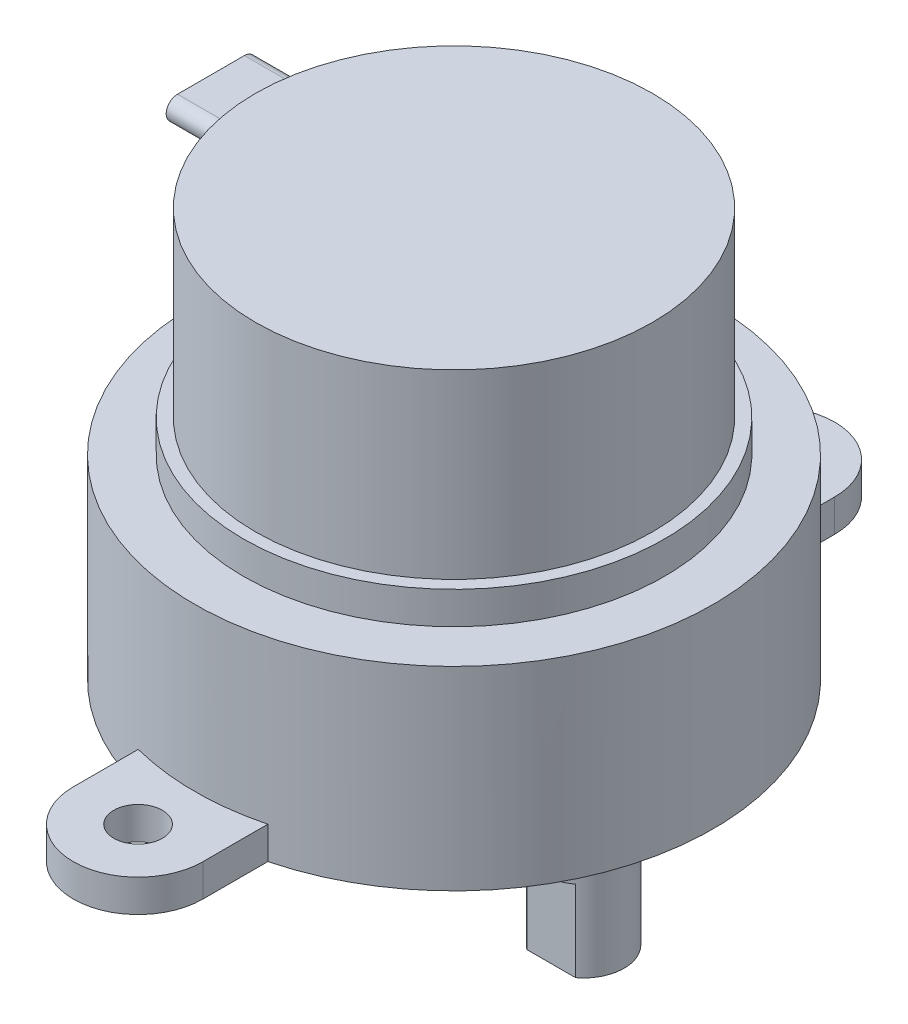
SolidWorks part; units mm, degrees
ref_plane "Front Plane" through (0, 0, 0) normal (0, 0, 1) x (1, 0, 0)
ref_plane "Top Plane" through (0, 0, 0) normal (0, 1, 0) x (1, 0, 0)
ref_plane "Right Plane" through (0, 0, 0) normal (1, 0, 0) x (0, 0, -1)
sketch "Sketch1" plane through (0, 0, 0) normal (0, 0, 1) x (1, 0, 0)
  line L0 (0, 0) -> (-21, 0) construction
  line L1 (0, 0) -> (0, 32.25) construction
  line L2 (0, 0) -> (-16, 0)
  line L3 (-16, 0) -> (-16, 12)
  line L4 (-16, 12) -> (-13, 12)
  line L5 (-13, 12) -> (-13, 14)
  line L6 (-13, 14) -> (-12.25, 14)
  line L7 (-12.25, 14) -> (-12.25, 25.2)
  line L8 (-12.25, 25.2) -> (0, 25.2)
  line L9 (0, 0) -> (0, 25.2)
  point P3 (-13, 13)
  dimension "D1" = 26
  dimension "D2" = 24.5
  dimension "D3" = 32
  dimension "D4" = 11.2
  dimension "D5" = 25.2
  dimension "D6" = 2
  dimension "D7" = 12
revolve "Revolve1" add sketch "Sketch1" angle 360 about L9
sketch "Sketch2" plane through (0, 0, 0) normal (0, 0, 1) x (1, 0, 0)
  line L0 (8, 0) -> (8, -10.2) construction
  line L1 (-16, 0) -> (16, 0) construction
  line L2 (4, -2.7) -> (4, -1.25)
  line L3 (4, -1.25) -> (3.5, -1.25)
  line L4 (3.5, -1.25) -> (3.5, 0)
  line L5 (4, -2.7) -> (5.5, -2.7)
  line L6 (5.5, -2.7) -> (5.5, -10.2)
  line L7 (5.5, -10.2) -> (8, -10.2)
  line L8 (3.5, 0) -> (8, 0)
  line L9 (8, 0) -> (8, -10.2)
  dimension "D1" = 5
  dimension "D2" = 8
  dimension "D3" = 8
  dimension "D4" = 2.7
  dimension "D5" = 10.2
  dimension "D6" = 9
  dimension "D7" = 1.25
revolve "Revolve2" add sketch "Sketch2" angle 360 about L0
hole_wizard "M3 Tapped Hole1" positions "Sketch3" profile "Sketch4" tap size "M3" standard "GB"
sketch "Sketch3" plane through (0, -10.2, 0) normal (0, -1, 0) x (-1, 0, 0)
  point P0 (-8, 0)
cosmetic thread "Hole Thread1" parameters "D1"=6, "D2"=3
sketch "Sketch4" plane through (8, -10.2, 0) normal (1, 0, 0) x (0, 0, -1)
  line L0 (0, 0) -> (0, 8.2511)
  line L1 (0, 8.2511) -> (1.25, 7.5)
  line L2 (1.25, 7.5) -> (1.25, 0)
  line L5 (1.25, 0) -> (0, 0)
  line L10 (0, 8.2511) -> (-1.25, 7.5) construction
  line L11 (0, -6.35) -> (0, 107.95) construction
  dimension "Tap Drill Dia." = 2.5
  dimension "Tap Drill Depth" = 7.5
  dimension "Drill Angle" = 118
sketch "Sketch5" plane through (0, -10.2, 0) normal (0, -1, 0) x (1, 0, 0)
  line L0 (8, 0) -> (19.5255, 0) construction
  line L1 (2.0409, 7.2169) -> (13.2652, 7.2169)
  line L2 (2.0409, 7.2169) -> (2.0409, 2)
  line L3 (2.0409, 2) -> (13.2652, 2)
  line L4 (13.2652, 7.2169) -> (13.2652, 2)
  line L5 (2.3255, -7.1853) -> (13.2652, -7.1853)
  line L6 (2.3255, -7.1853) -> (2.3255, -2)
  line L7 (2.3255, -2) -> (13.2652, -2)
  line L8 (13.2652, -7.1853) -> (13.2652, -2)
  dimension "D1" = 4
extrude "Cut-Extrude1" cut sketch "Sketch5" against normal blind 5
sketch "Sketch6" plane through (0, 0, 0) normal (0, -1, 0) x (1, 0, 0)
  line L0 (0, -19.5) -> (0, 19.5) construction
  line L1 (-4, -19.5) -> (-4, 19.5)
  line L2 (4, -19.5) -> (4, 19.5)
  arc A0 (-4, -19.5) -> (4, -19.5) centre (0, -19.5) ccw
  arc A1 (4, 19.5) -> (-4, 19.5) centre (0, 19.5) ccw
  circle A2 centre (0, -19.5) radius 1.5
  circle A3 centre (0, 19.5) radius 1.5
  point P2 (0, 0)
  dimension "D3" = 3
  dimension "D1" = 8
  dimension "D2" = 39
extrude "Boss-Extrude1" add sketch "Sketch6" against normal blind 2
sketch "Sketch7" plane through (0, 0, 0) normal (1, 0, 0) x (0, 0, -1)
  line L0 (0, 25.2) -> (0, 24.1102)
  line L1 (12.25, 25.2) -> (-12.25, 25.2) construction
  line L2 (-2.0653, 24.1102) -> (2.0653, 24.1102) construction
  line L3 (-2.0653, 24.8103) -> (2.0653, 24.8103)
  line L4 (-2.0653, 23.4101) -> (2.0653, 23.4101)
  arc A0 (-2.0653, 24.8103) -> (-2.0653, 23.4101) centre (-2.0653, 24.1102) ccw
  arc A1 (2.0653, 23.4101) -> (2.0653, 24.8103) centre (2.0653, 24.1102) ccw
  point P7 (0, 24.1102)
extrude "Boss-Extrude2" add sketch "Sketch7" against normal blind 15 contours L3 A1 L4 A0
